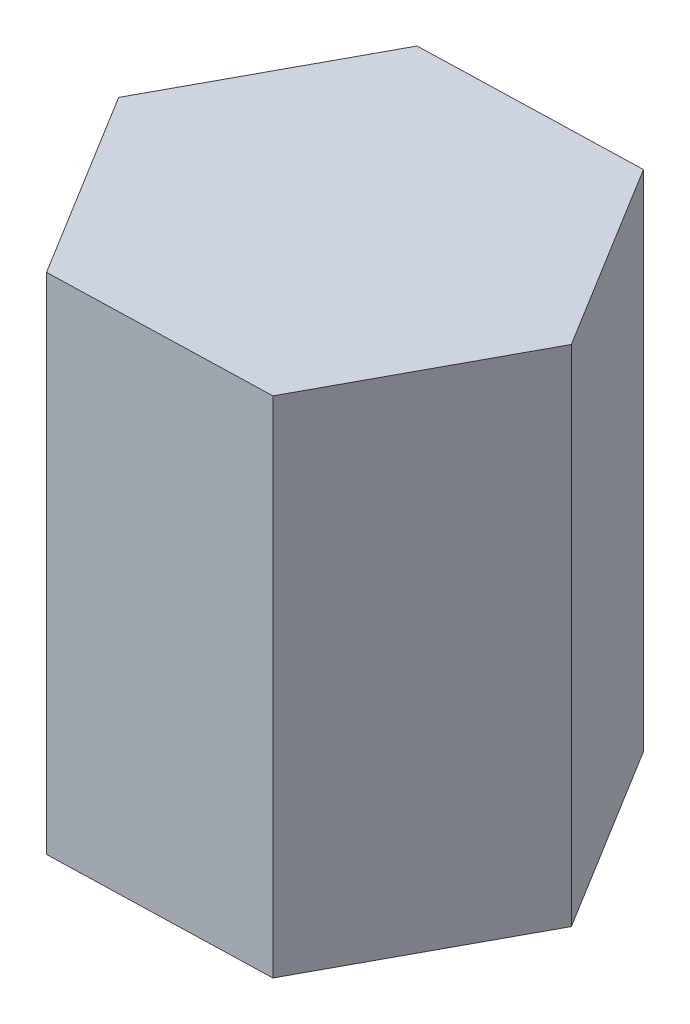
SolidWorks part; units mm, degrees
ref_plane "Front" through (0, 0, 0) normal (0, 0, 1) x (1, 0, 0)
ref_plane "Top" through (0, 0, 0) normal (0, 1, 0) x (1, 0, 0)
ref_plane "Right" through (0, 0, 0) normal (1, 0, 0) x (0, 0, -1)
sketch "草图1" plane through (0, 0, 0) normal (0, 1, 0) x (1, 0, 0)
  line L1 (20.7681, 38.4345) -> (-22.9012, 37.203)
  line L2 (-22.9012, 37.203) -> (-43.6693, -1.2315)
  line L3 (-43.6693, -1.2315) -> (-20.7681, -38.4345)
  line L4 (-20.7681, -38.4345) -> (22.9012, -37.203)
  line L5 (22.9012, -37.203) -> (43.6693, 1.2315)
  line L6 (43.6693, 1.2315) -> (20.7681, 38.4345)
  circle A0 centre (0, 0) radius 37.8338 construction
extrude "凸台-拉伸1" add sketch "草图1" along normal blind 100
sketch "草图2" plane through (0, 100, 0) normal (0, 1, 0) x (1, 0, 0)
  circle A0 centre (0, 0) radius 12.8693
extrude "切除-拉伸1" [suppressed] cut sketch "草图2" against normal through all
